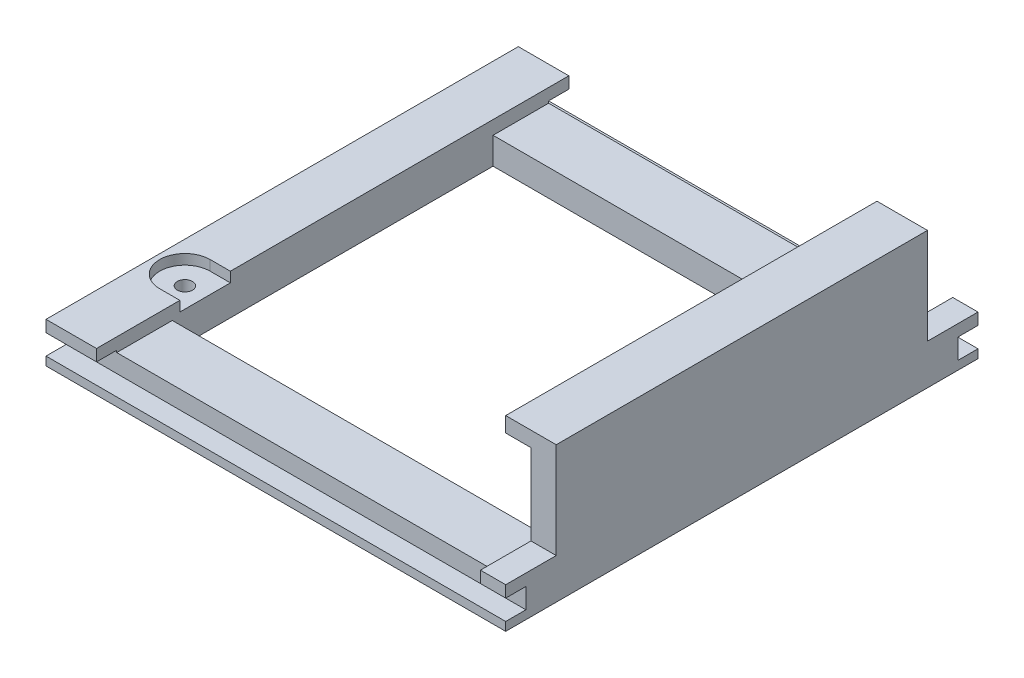
SolidWorks part; units mm, degrees
ref_plane "Plan de face" through (0, 0, 0) normal (0, 0, 1) x (1, 0, 0)
ref_plane "Plan de dessus" through (0, 0, 0) normal (0, 1, 0) x (1, 0, 0)
ref_plane "Plan de droite" through (0, 0, 0) normal (1, 0, 0) x (0, 0, -1)
sketch "Esquisse1" plane through (0, 0, 0) normal (0, 1, 0) x (1, 0, 0)
  line L0 (-48, 36.75) -> (-48, -36.75)
  line L1 (-38, -31.75) -> (38, -31.75)
  line L2 (-38, -31.75) -> (-38, 31.75)
  line L3 (-38, 31.75) -> (38, 31.75)
  line L4 (38, -31.75) -> (38, 31.75)
  line L5 (-38, -31.75) -> (38, 31.75) construction
  line L6 (-38, 31.75) -> (38, -31.75) construction
  line L7 (-48, -36.75) -> (43, -36.75)
  line L8 (43, -36.75) -> (43, 36.75)
  line L9 (43, 36.75) -> (-48, 36.75)
  circle A0 centre (-42, -25.25) radius 1.5
  point P0 (0, 0)
  dimension "D9" = 3
  dimension "D1" = 63.5
  dimension "D2" = 76
  dimension "D3" = 5
  dimension "D4" = 10
  dimension "D5" = 5
  dimension "D6" = 5
  dimension "D7" = 11.5
  dimension "D8" = 4
extrude "Boss.-Extru.1" add sketch "Esquisse1" along normal blind 8
sketch "Esquisse2" plane through (0, 8, 0) normal (0, 1, 0) x (1, 0, 0)
  line L0 (-42, -30.25) -> (-38, -30.25)
  line L1 (-38, 31.75) -> (-38, -31.75) construction
  line L2 (-38, -30.25) -> (-38, -20.25)
  line L3 (-38, -20.25) -> (-42, -20.25)
  arc A0 (-42, -20.25) -> (-42, -30.25) centre (-42, -25.25) ccw
  dimension "D1" = 10
extrude "Enlèv. mat.-Extru.1" cut sketch "Esquisse2" against normal blind 2
sketch "Esquisse3" plane through (0, 8, 0) normal (0, 1, 0) x (1, 0, 0)
  line L0 (-48, -36.75) -> (43, -36.75) construction
  line L1 (38, -31.75) -> (-38, -31.75)
  line L2 (38, -31.75) -> (38, -36.75)
  line L3 (38, -36.75) -> (-38, -36.75)
  line L4 (-38, -31.75) -> (-38, -36.75)
  line L5 (43, 36.75) -> (-48, 36.75) construction
  line L6 (38, 31.75) -> (-38, 31.75)
  line L7 (38, 31.75) -> (38, 36.75)
  line L8 (38, 36.75) -> (-38, 36.75)
  line L9 (-38, 31.75) -> (-38, 36.75)
  line L11 (-38, 31.75) -> (-38, -20.25) construction
  point P16 (79.6693, 4.9139)
extrude "Enlèv. mat.-Extru.2" cut sketch "Esquisse3" against normal blind 2.7
sketch "Esquisse4" plane through (0, 0, -36.75) normal (0, 0, -1) x (-1, 0, 0)
  line L0 (-38, 5.3) -> (38, 5.3) construction
  line L1 (-43, 8) -> (-38, 8)
  line L2 (-43, 8) -> (-43, 27)
  line L3 (-43, 27) -> (-38.8159, 27)
  line L4 (-38, 8) -> (-38, 24)
  line L5 (-38.8159, 27) -> (-33, 27)
  line L7 (-38, 24) -> (-33, 24)
  line L8 (-33, 27) -> (-33, 24)
  dimension "D1" = 5
  dimension "D2" = 18.7
  dimension "D3" = 3
  dimension "D4" = 5
extrude "Boss.-Extru.2" add sketch "Esquisse4" against normal up to surface (73.5 mm away) up to face at (-1.25, 5.325, 36.75)
sketch "Esquisse5" plane through (0, 0, 0) normal (0, -1, 0) x (1, 0, 0)
  line L1 (43, -36.75) -> (-48, -36.75)
  line L2 (43, -36.75) -> (43, -46.75)
  line L3 (43, -46.75) -> (-48, -46.75)
  line L4 (-48, -36.75) -> (-48, -46.75)
  line L5 (43, 36.75) -> (-48, 36.75)
  line L6 (43, 36.75) -> (43, 46.75)
  line L7 (43, 46.75) -> (-48, 46.75)
  line L8 (-48, 36.75) -> (-48, 46.75)
  dimension "D1" = 91
  dimension "D2" = 10
  dimension "D3" = 10
  dimension "D4" = 91
extrude "Boss.-Extru.3" add sketch "Esquisse5" against normal up to surface (5.3 mm away) up to face at (0, 5.3, -34.25)
sketch "Esquisse6" plane through (0, 5.3, 0) normal (0, 1, 0) x (1, 0, 0)
  line L0 (43, -36.75) -> (33, -36.75) construction
  line L1 (43, 46.75) -> (38, 46.75)
  line L2 (43, 46.75) -> (43, 36.75)
  line L3 (43, 36.75) -> (38, 36.75)
  line L4 (38, 46.75) -> (38, 36.75)
  line L5 (43, -46.75) -> (38, -46.75)
  line L6 (43, -46.75) -> (43, -36.75)
  line L7 (43, -36.75) -> (38, -36.75)
  line L8 (38, -46.75) -> (38, -36.75)
  line L10 (-38, 36.75) -> (-48, 36.75)
  line L11 (-38, 36.75) -> (-38, 46.75)
  line L12 (-38, 46.75) -> (-48, 46.75)
  line L13 (-48, 36.75) -> (-48, 46.75)
  line L14 (-38, -36.75) -> (-48, -36.75)
  line L15 (-38, -36.75) -> (-38, -46.75)
  line L16 (-38, -46.75) -> (-48, -46.75)
  line L17 (-48, -36.75) -> (-48, -46.75)
extrude "Boss.-Extru.4" add sketch "Esquisse6" along normal up to surface (2.7 mm away) up to face at (-42.125, 8, 12.625)
sketch "Esquisse7" plane through (-48, 0, 0) normal (-1, 0, 0) x (0, 0, 1)
  line L0 (-46.75, 8) -> (-46.75, 0) construction
  line L1 (-46.75, 1.7) -> (-42.75, 1.7)
  line L2 (-46.75, 1.7) -> (-46.75, 5.7)
  line L3 (-46.75, 5.7) -> (-42.75, 5.7)
  line L4 (-42.75, 1.7) -> (-42.75, 5.7)
  line L5 (46.75, 8) -> (46.75, 0) construction
  line L6 (46.75, 1.7) -> (42.75, 1.7)
  line L7 (46.75, 1.7) -> (46.75, 5.7)
  line L8 (46.75, 5.7) -> (42.75, 5.7)
  line L9 (42.75, 1.7) -> (42.75, 5.7)
  line L10 (-46.75, 0) -> (46.75, 0) construction
  dimension "D1" = 1.7
  dimension "D2" = 4
  dimension "D3" = 4
  dimension "D4" = 1.7
  dimension "D5" = 4
  dimension "D6" = 4
extrude "Enlèv. mat.-Extru.3" cut sketch "Esquisse7" against normal through all
